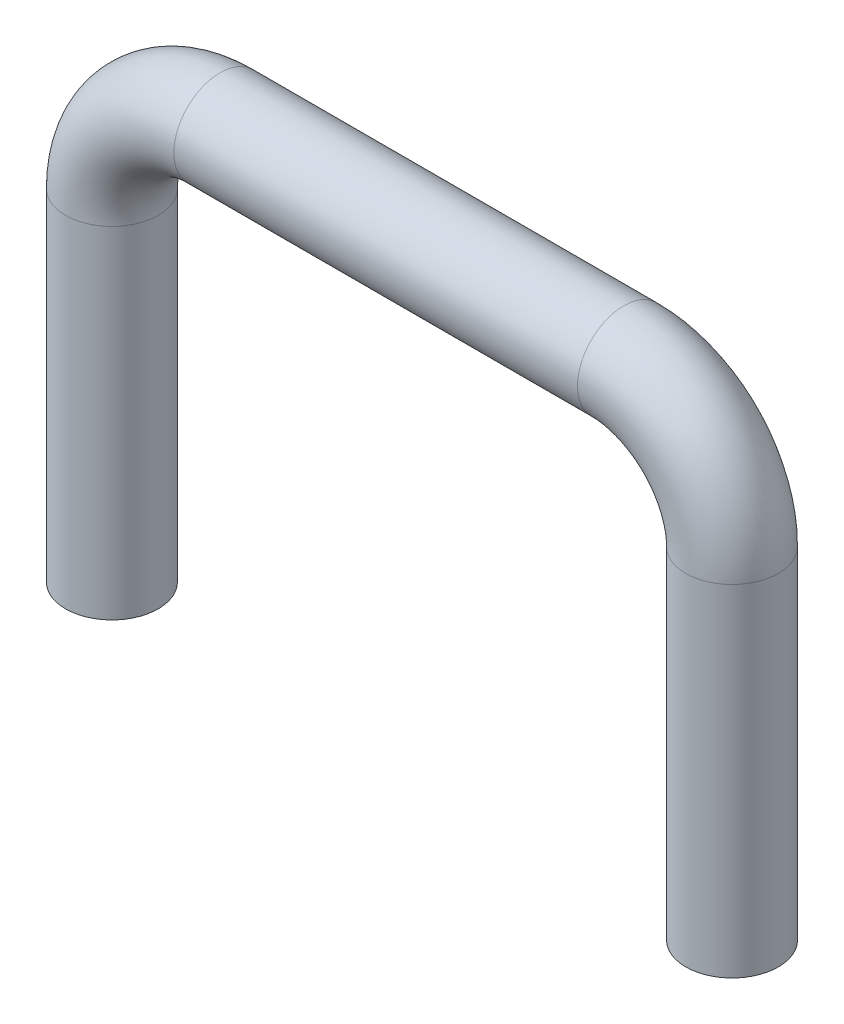
SolidWorks part; units mm, degrees
material "Plain Carbon Steel"
ref_plane "Front Plane" through (0, 0, 0) normal (0, 0, 1) x (1, 0, 0)
ref_plane "Top Plane" through (0, 0, 0) normal (0, 1, 0) x (1, 0, 0)
ref_plane "Right Plane" through (0, 0, 0) normal (1, 0, 0) x (0, 0, -1)
sketch "Sketch2" plane through (0, 0, 0) normal (0, 0, 1) x (1, 0, 0)
  line L0 (0, 25.4) -> (-10.35, 25.4)
  line L1 (-18.2748, 17.4752) -> (-18.2748, 0)
  line L2 (-18.2748, 0) -> (-13.525, 0) construction
  line L3 (0, 25.4) -> (0, 20.6502) construction
  line L4 (0, 20.6502) -> (-10.35, 20.6502)
  line L5 (-13.525, 17.4752) -> (-13.525, 0)
  line L6 (-15.8999, 0) -> (-15.8999, 17.4752) construction
  line L7 (-10.35, 23.0251) -> (0, 23.0251) construction
  arc A0 (-10.35, 25.4) -> (-18.2748, 17.4752) centre (-10.35, 17.4752) ccw
  arc A1 (-10.35, 20.6502) -> (-13.525, 17.4752) centre (-10.35, 17.4752) ccw
  arc A2 (-15.8999, 17.4752) -> (-10.35, 23.0251) centre (-10.35, 17.4752) cw construction
  dimension "D4" = 3.175
  dimension "D1" = 27.05
  dimension "D2" = 25.4
  dimension "D3" = 4.7498
sketch "Sketch3" plane through (0, 0, 0) normal (0, 1, 0) x (1, 0, 0)
  line L0 (-18.2748, 0) -> (-13.525, 0) construction
  circle A0 centre (-15.8999, 0) radius 2.3749
sketch "Sketch4" plane through (0, 0, 0) normal (0, 0, 1) x (1, 0, 0)
  line L0 (-10.35, 23.0251) -> (0, 23.0251) construction
  line L1 (-15.8999, 0) -> (-15.8999, 17.4752) construction
  line L2 (-10.35, 23.0251) -> (0, 23.0251)
  line L3 (-15.8999, 0) -> (-15.8999, 17.4752)
  arc A0 (-10.35, 23.0251) -> (-15.8999, 17.4752) centre (-10.35, 17.4752) ccw construction
  arc A1 (-10.35, 23.0251) -> (-15.8999, 17.4752) centre (-10.35, 17.4752) ccw
sweep "Sweep1" add profiles "Sketch3" path "Sketch4"
mirror "Mirror1" about plane through (0, 0, 0) normal (1, 0, 0) of bodies 101
